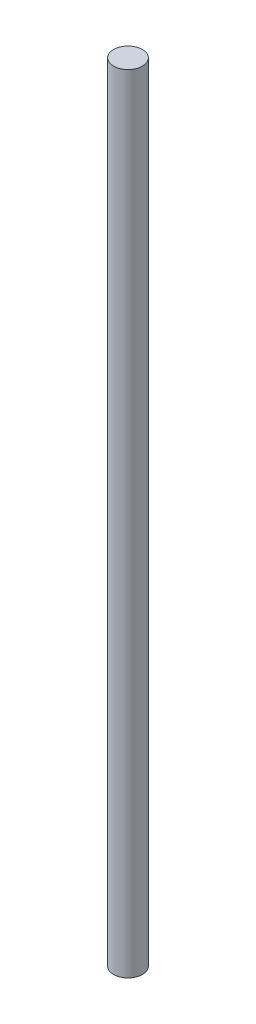
SolidWorks part; units mm, degrees
ref_plane "Front Plane" through (0, 0, 0) normal (0, 0, 1) x (1, 0, 0)
ref_plane "Top Plane" through (0, 0, 0) normal (0, 1, 0) x (1, 0, 0)
ref_plane "Right Plane" through (0, 0, 0) normal (1, 0, 0) x (0, 0, -1)
sketch "Sketch1" plane through (0, 0, 0) normal (0, 1, 0) x (1, 0, 0)
  circle A0 centre (0, 0) radius 11
  dimension "D1" = 22
extrude "Boss-Extrude1" add sketch "Sketch1" along normal blind 600
